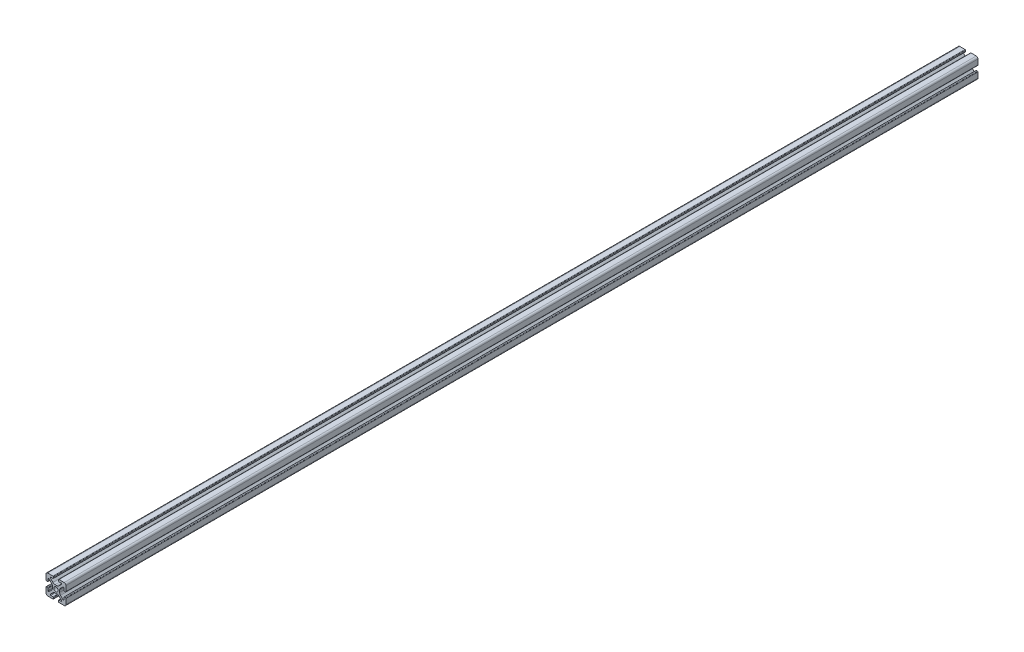
SolidWorks part; units mm, degrees
ref_plane "Front Plane" through (0, 0, 0) normal (0, 0, 1) x (1, 0, 0)
ref_plane "Top Plane" through (0, 0, 0) normal (0, 1, 0) x (1, 0, 0)
ref_plane "Right Plane" through (0, 0, 0) normal (1, 0, 0) x (0, 0, -1)
sketch "Sketch2" plane through (0, 0, 0) normal (0, 0, 1) x (1, 0, 0)
  line L0 (0, 10) -> (0, -10) construction
  line L1 (-10, 0) -> (10, 0) construction
  line L2 (2.5, -10) -> (10, -10)
  line L3 (10, -10) -> (10, -2.5)
  line L4 (2.5, -10) -> (2.5, -7.9246)
  line L5 (2.5, -7.9246) -> (6.4571, -7.9246)
  line L6 (6.4571, -7.9246) -> (2.1325, -3.6)
  line L7 (0, 0) -> (10, -10) construction
  line L8 (10, -2.5) -> (7.9246, -2.5)
  line L9 (7.9246, -2.5) -> (7.9246, -6.4571)
  line L10 (7.9246, -6.4571) -> (3.6, -2.1325)
  line L11 (5.7623, -4.2948) -> (4.2948, -5.7623) construction
  circle A0 centre (0, 0) radius 2.15
  arc A1 (5.25, -7.9246) -> (5.6036, -7.0711) centre (5.25, -7.4246) ccw construction
  point P8 (0, -3.6)
  point P16 (5.0286, -5.0286)
  dimension "Center Hole Diameter" = 4.3
  dimension "D3" = 0.5
  dimension "Rail Height" = 20
  dimension "Rail Width" = 20
  dimension "T-Slot Width" = 5
  dimension "Slot Depth" = 6.4
  dimension "Slot Inner Width" = 11.5
sketch "Sketch3" plane through (0, 0, 0) normal (1, 0, 0) x (0, 0, -1)
  line L0 (-457.2, -10) -> (457.2, -10) construction
  line L1 (-431.8, 0) -> (431.8, 0) construction
  line L2 (0, 10) -> (0, -10) construction
  line L3 (0, 10) -> (0, -10) construction
  point P6 (-431.8, 0)
  point P8 (431.8, 0)
  dimension "Length" = 914.4
  dimension "D1" = 25.4
sketch "Sketch4" plane through (0, 0, 0) normal (0, 0, 1) x (1, 0, 0)
  line L0 (3, -10) -> (8.25, -10)
  line L1 (2.5, -10) -> (10, -10) construction
  line L2 (2.5, -10) -> (2.5, -7.9246) construction
  line L3 (2.5, -7.9246) -> (6.4571, -7.9246) construction
  line L4 (2.5, -8.4246) -> (2.5, -9.5)
  line L5 (3, -7.9246) -> (5.25, -7.9246)
  line L6 (0, -3.6) -> (0.8898, -3.6)
  line L7 (6.4571, -7.9246) -> (2.1325, -3.6) construction
  line L8 (3.0112, -4.4787) -> (5.6036, -7.0711)
  line L9 (10, -10) -> (10, -2.5) construction
  line L10 (7.9246, -6.4571) -> (3.6, -2.1325) construction
  line L11 (7.9246, -2.5) -> (7.9246, -6.4571) construction
  line L12 (7.9246, -5.25) -> (7.9246, -3)
  line L13 (10, -2.5) -> (7.9246, -2.5) construction
  line L14 (8.4246, -2.5) -> (9.5, -2.5)
  line L15 (10, -3) -> (10, -8.25)
  line L16 (7.0711, -5.6036) -> (4.4787, -3.0112)
  line L17 (3.6, 0) -> (3.6, -0.8898)
  line L18 (-10, 0) -> (10, 0) construction
  line L19 (0, -3.6) -> (0, -2.15)
  line L20 (0, 10) -> (0, -10) construction
  line L21 (3.6, 0) -> (2.15, 0)
  arc A0 (2.5, -9.5) -> (3, -10) centre (3, -9.5) ccw
  arc A1 (5.25, -7.9246) -> (5.6036, -7.0711) centre (5.25, -7.4246) ccw construction
  arc A2 (2.5, -8.4246) -> (3, -7.9246) centre (3, -8.4246) cw
  arc A3 (5.25, -7.9246) -> (5.6036, -7.0711) centre (5.25, -7.4246) ccw
  arc A4 (0.8898, -3.6) -> (3.0112, -4.4787) centre (0.8898, -6.6) cw
  arc A5 (8.25, -10) -> (10, -8.25) centre (8.25, -8.25) ccw
  arc A6 (7.0711, -5.6036) -> (7.9246, -5.25) centre (7.4246, -5.25) ccw
  arc A7 (7.9246, -3) -> (8.4246, -2.5) centre (8.4246, -3) cw
  arc A8 (9.5, -2.5) -> (10, -3) centre (9.5, -3) cw
  arc A9 (4.4787, -3.0112) -> (3.6, -0.8898) centre (6.6, -0.8898) cw
  circle A10 centre (0, 0) radius 2.15 construction
  arc A11 (0, -2.15) -> (2.15, 0) centre (0, 0) ccw
  dimension "D1" = 1.75
  dimension "D2" = 3
extrude "Boss-Extrude1" add sketch "Sketch4" along normal mid plane 914.4
mirror "Mirror1" about plane through (0, 0, 0) normal (1, 0, 0) of bodies 134
mirror "Mirror2" about plane through (0, 0, 0) normal (0, 1, 0) of bodies 135
equation "\"D3@Sketch2\"=\"T-Slot Width@Sketch2\"*0.1"
equation "\"D1@Sketch4\"=\"D3@Sketch2\"*3.5"
equation "\"D2@Sketch4\"=\"D3@Sketch2\"*6"
equation "\"D1@Boss-Extrude1\"=\"Length@Sketch3\""
